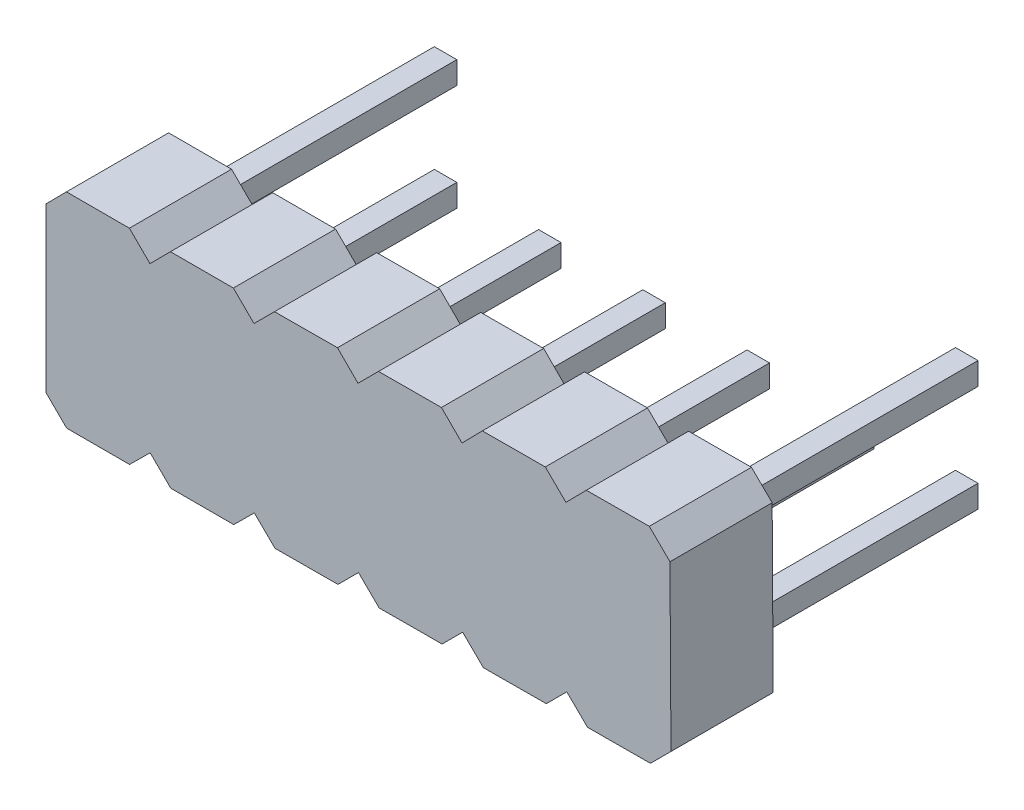
SolidWorks part; units mm, degrees
ref_plane "Front Plane" through (0, 0, 0) normal (0, 0, 1) x (1, 0, 0)
ref_plane "Top Plane" through (0, 0, 0) normal (0, 1, 0) x (1, 0, 0)
ref_plane "Right Plane" through (0, 0, 0) normal (1, 0, 0) x (0, 0, -1)
sketch "Sketch1" plane through (0, 0, 0) normal (0, 0, 1) x (1, 0, 0)
  line L0 (0, 0) -> (0, 4)
  line L1 (0, 4) -> (0.5, 4.5041)
  line L2 (0.5, 4.5041) -> (2.04, 4.5041)
  line L3 (2.04, 4.5041) -> (2.5441, 4.0041)
  line L4 (2.5441, 4.0041) -> (3.0441, 4.5082)
  line L5 (3.0441, 4.5082) -> (4.5841, 4.5082)
  line L6 (4.5841, 4.5082) -> (5.0882, 4.0082)
  line L7 (0, 0) -> (0.5041, -0.5)
  line L8 (0.5041, -0.5) -> (2.0441, -0.5)
  line L9 (2.0441, -0.5) -> (2.5482, 0)
  line L10 (2.5482, 0) -> (3.0522, -0.5)
  line L11 (3.0522, -0.5) -> (4.5922, -0.5)
  line L12 (4.5922, -0.5) -> (5.0963, 0)
  line L13 (14.7869, -0.4605) -> (15.2889, 0.0415)
  line L14 (5.5902, 4.5102) -> (5.0882, 4.0082)
  line L15 (5.6024, -0.4979) -> (5.0963, 0)
  line L16 (7.1424, -0.4917) -> (5.6024, -0.4979)
  line L17 (7.6445, 0.0104) -> (7.1424, -0.4917)
  line L18 (8.1506, -0.4876) -> (7.6445, 0.0104)
  line L19 (9.6906, -0.4813) -> (8.1506, -0.4876)
  line L20 (10.1926, 0.0208) -> (9.6906, -0.4813)
  line L21 (7.1302, 4.5165) -> (5.5902, 4.5102)
  line L22 (7.6322, 4.0145) -> (7.1302, 4.5165)
  line L23 (8.1343, 4.5165) -> (7.6322, 4.0145)
  line L24 (9.6743, 4.5228) -> (8.1343, 4.5165)
  line L25 (10.1763, 4.0207) -> (9.6743, 4.5228)
  line L27 (13.2469, -0.4668) -> (14.7869, -0.4605)
  line L28 (12.7408, 0.0312) -> (13.2469, -0.4668)
  line L29 (12.2387, -0.4709) -> (12.7408, 0.0312)
  line L30 (10.6987, -0.4772) -> (12.2387, -0.4709)
  line L31 (10.1926, 0.0208) -> (10.6987, -0.4772)
  line L32 (10.1763, 4.0207) -> (10.6743, 4.5269)
  line L33 (10.6743, 4.5269) -> (12.2143, 4.5331)
  line L34 (12.2143, 4.5331) -> (12.7204, 4.0352)
  line L35 (12.7204, 4.0352) -> (13.2183, 4.5413)
  line L36 (13.2183, 4.5413) -> (14.7583, 4.5476)
  line L37 (14.7583, 4.5476) -> (15.2644, 4.0496)
  line L38 (15.2644, 4.0496) -> (15.2889, 0.0415)
extrude "Boss-Extrude1" add sketch "Sketch1" along normal blind 2.5
sketch "Sketch2" plane through (0, 0, 0) normal (0, 0, 1) x (1, 0, 0)
  line L1 (1, 0.98) -> (1.55, 0.98)
  line L2 (1, 0.98) -> (1, 0.43)
  line L3 (1, 0.43) -> (1.55, 0.43)
  line L4 (1.55, 0.98) -> (1.55, 0.43)
  line L5 (1, 0.98) -> (1.55, 0.43) construction
  line L6 (1, 0.43) -> (1.55, 0.98) construction
  line L10 (3.55, 0.98) -> (4.1, 0.98)
  line L11 (4.1, 0.98) -> (4.1, 0.43)
  line L12 (3.55, 0.43) -> (4.1, 0.43)
  line L13 (3.55, 0.98) -> (3.55, 0.43)
  line L14 (6.1, 0.98) -> (6.65, 0.98)
  line L15 (6.65, 0.98) -> (6.65, 0.43)
  line L16 (6.1, 0.43) -> (6.65, 0.43)
  line L17 (6.1, 0.98) -> (6.1, 0.43)
  line L18 (8.65, 0.98) -> (9.2, 0.98)
  line L19 (9.2, 0.98) -> (9.2, 0.43)
  line L20 (8.65, 0.43) -> (9.2, 0.43)
  line L21 (8.65, 0.98) -> (8.65, 0.43)
  line L22 (11.2, 0.98) -> (11.75, 0.98)
  line L23 (11.75, 0.98) -> (11.75, 0.43)
  line L24 (11.2, 0.43) -> (11.75, 0.43)
  line L25 (11.2, 0.98) -> (11.2, 0.43)
  line L26 (13.75, 0.98) -> (14.3, 0.98)
  line L27 (14.3, 0.98) -> (14.3, 0.43)
  line L28 (13.75, 0.43) -> (14.3, 0.43)
  line L29 (13.75, 0.98) -> (13.75, 0.43)
  line L30 (3.55, 3.58) -> (4.1, 3.58)
  line L31 (4.1, 3.58) -> (4.1, 3.03)
  line L32 (3.55, 3.03) -> (4.1, 3.03)
  line L33 (3.55, 3.58) -> (3.55, 3.03)
  line L34 (6.1, 3.58) -> (6.65, 3.58)
  line L35 (6.65, 3.58) -> (6.65, 3.03)
  line L36 (6.1, 3.03) -> (6.65, 3.03)
  line L37 (6.1, 3.58) -> (6.1, 3.03)
  line L38 (8.65, 3.58) -> (9.2, 3.58)
  line L39 (9.2, 3.58) -> (9.2, 3.03)
  line L40 (8.65, 3.03) -> (9.2, 3.03)
  line L41 (8.65, 3.58) -> (8.65, 3.03)
  line L42 (11.2, 3.58) -> (11.75, 3.58)
  line L43 (11.75, 3.58) -> (11.75, 3.03)
  line L44 (11.2, 3.03) -> (11.75, 3.03)
  line L45 (11.2, 3.58) -> (11.2, 3.03)
  line L46 (13.75, 3.58) -> (14.3, 3.58)
  line L47 (14.3, 3.58) -> (14.3, 3.03)
  line L48 (13.75, 3.03) -> (14.3, 3.03)
  line L49 (13.75, 3.58) -> (13.75, 3.03)
  line L50 (1, 3.58) -> (1.55, 3.58)
  line L51 (1.55, 3.58) -> (1.55, 3.03)
  line L52 (1, 3.03) -> (1.55, 3.03)
  line L53 (1, 3.58) -> (1, 3.03)
  point P0 (1.275, 0.705)
  point P5 (0, 0)
  dimension "D2" = 6
  dimension "D3" = 2
extrude "Boss-Extrude2" add sketch "Sketch2" against normal blind 6 contours L14 L17 L16 L15 | L10 L13 L12 L11 | L26 L29 L28 L27 | L46 L49 L48 L47 | L19 L20 L21 L18 | L2 L3 L4 L1 | L25 L24 L23 L22 | L50 L51 L52 L53
